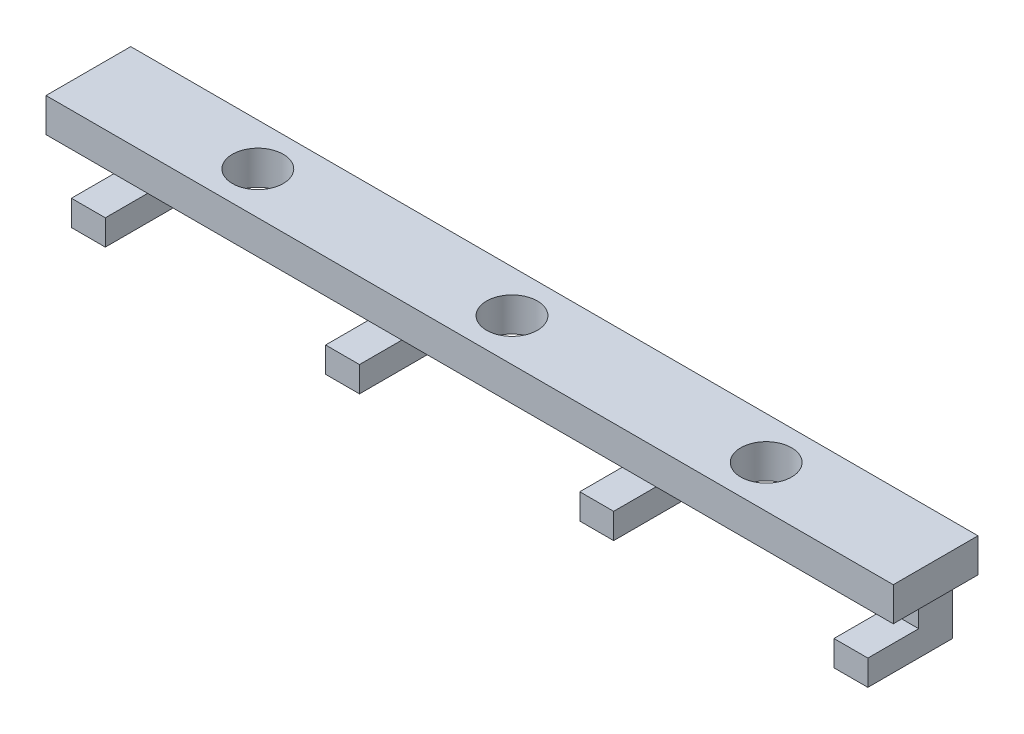
SolidWorks part; units mm, degrees
ref_plane "Front Plane" through (0, 0, 0) normal (0, 0, 1) x (1, 0, 0)
ref_plane "Top Plane" through (0, 0, 0) normal (0, 1, 0) x (1, 0, 0)
ref_plane "Right Plane" through (0, 0, 0) normal (1, 0, 0) x (0, 0, -1)
sketch "Sketch1" plane through (0, 0, 0) normal (0, 1, 0) x (1, 0, 0)
  line L1 (-31.75, -3.175) -> (31.75, -3.175)
  line L2 (-31.75, -3.175) -> (-31.75, 3.175)
  line L3 (-31.75, 3.175) -> (31.75, 3.175)
  line L4 (31.75, -3.175) -> (31.75, 3.175)
  line L5 (-31.75, -3.175) -> (31.75, 3.175) construction
  line L6 (-31.75, 3.175) -> (31.75, -3.175) construction
  line L7 (0, 3.175) -> (0, -3.175) construction
  circle A0 centre (0, 0) radius 1.905
  circle A2 centre (-19.05, 0) radius 1.905
  circle A3 centre (19.05, 0) radius 1.905
  point P0 (0, 0)
  point P16 (-15.875, 0)
  dimension "D3" = 3.81
  dimension "D1" = 63.5
  dimension "D2" = 6.35
  dimension "D4" = 19.05
extrude "Boss-Extrude1" add sketch "Sketch1" along normal blind 2.54
sketch "Sketch2" plane through (0, 0, 0) normal (0, -1, 0) x (1, 0, 0)
  line L0 (-8.255, -3.175) -> (-8.255, 3.175)
  line L5 (-8.255, -3.175) -> (-10.795, -3.175)
  line L10 (-10.795, -3.175) -> (-10.795, 3.175)
  line L11 (31.75, -3.175) -> (-31.75, -3.175) construction
  line L12 (-27.305, -3.175) -> (-29.845, -3.175)
  line L13 (-27.305, -3.175) -> (-27.305, 3.175)
  line L14 (-27.305, 3.175) -> (-29.845, 3.175)
  line L15 (-29.845, -3.175) -> (-29.845, 3.175)
  line L16 (-27.305, -3.175) -> (-29.845, 3.175) construction
  line L17 (-27.305, 3.175) -> (-29.845, -3.175) construction
  line L18 (-8.255, 3.175) -> (-10.795, 3.175)
  line L19 (10.795, -3.175) -> (10.795, 3.175)
  line L20 (10.795, -3.175) -> (8.255, -3.175)
  line L21 (8.255, -3.175) -> (8.255, 3.175)
  line L22 (10.795, 3.175) -> (8.255, 3.175)
  line L23 (29.845, -3.175) -> (29.845, 3.175)
  line L24 (29.845, -3.175) -> (27.305, -3.175)
  line L25 (27.305, -3.175) -> (27.305, 3.175)
  line L26 (29.845, 3.175) -> (27.305, 3.175)
  line L29 (-31.75, 3.175) -> (31.75, 3.175) construction
  line L30 (-27.305, 0) -> (27.305, 0) construction
  point P0 (-28.575, 0)
  point P24 (0, 0)
  dimension "D1" = 2.54
  dimension "D3" = 19.05
  dimension "D2" = 4
extrude "Boss-Extrude2" add sketch "Sketch2" along normal blind 5.08
sketch "Sketch3" plane through (0, 0, 3.175) normal (0, 0, 1) x (1, 0, 0)
  line L0 (-31.75, 2.54) -> (-31.75, 0) construction
  line L1 (-31.75, 0) -> (31.75, 0)
  line L2 (-31.75, 0) -> (-31.75, -3.175)
  line L3 (-31.75, -3.175) -> (31.75, -3.175)
  line L4 (31.75, 0) -> (31.75, -3.175)
  line L5 (31.75, 2.54) -> (31.75, 0) construction
  line L6 (-27.305, 0) -> (-10.795, 0) construction
  dimension "D1" = 3.175
extrude "Cut-Extrude1" cut sketch "Sketch3" against normal blind 3.81
